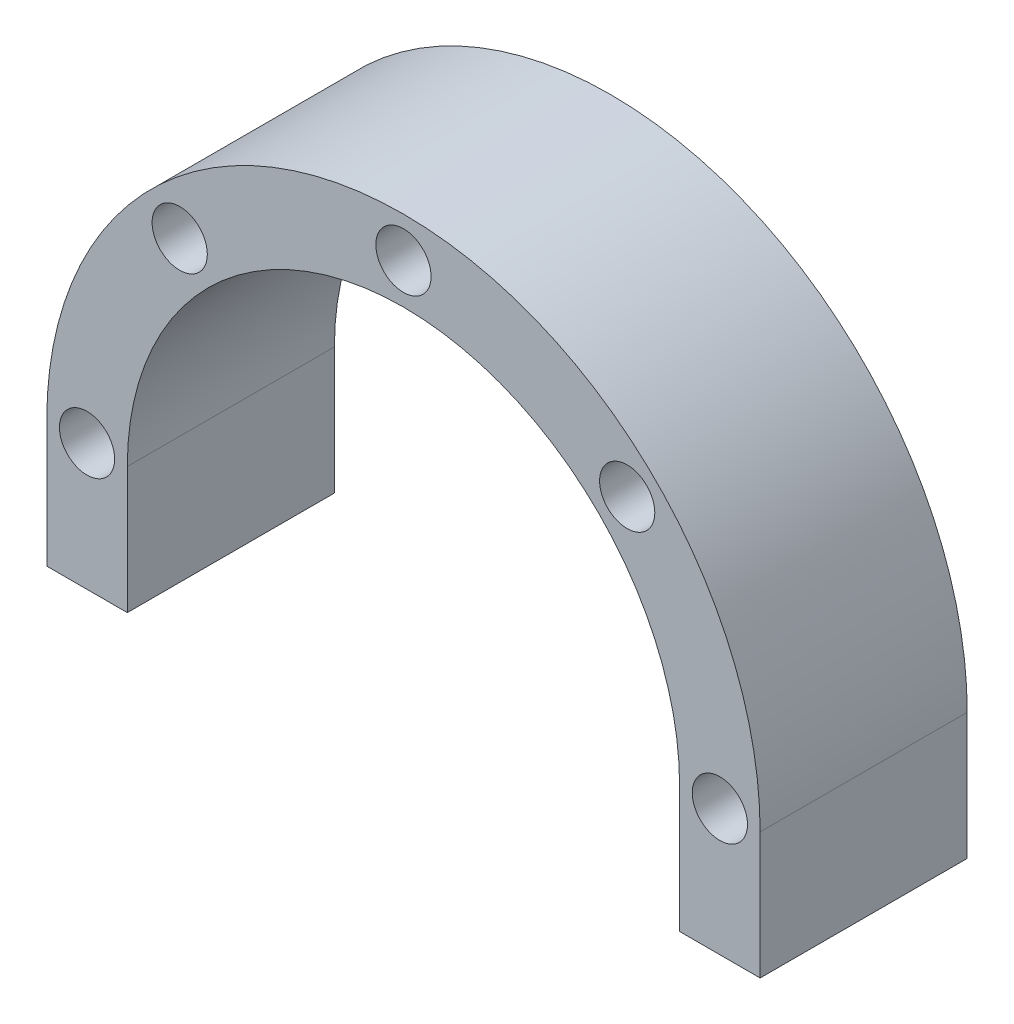
SolidWorks part; units mm, degrees
material "ABS"
ref_plane "正面" through (0, 0, 0) normal (0, 0, 1) x (1, 0, 0)
ref_plane "平面" through (0, 0, 0) normal (0, 1, 0) x (1, 0, 0)
ref_plane "右側面" through (0, 0, 0) normal (1, 0, 0) x (0, 0, -1)
sketch "ｽｹｯﾁ1" plane through (0, 0, 0) normal (0, 0, 1) x (1, 0, 0)
  line L0 (0, -1000) -> (0, 49000) construction
  line L1 (-31, -11) -> (31, -11)
  line L2 (-31, 0) -> (-31, -11)
  line L4 (31, -11) -> (31, 0)
  circle A0 centre (0, 0) radius 31 construction
  arc A2 (-31, 0) -> (31, 0) centre (0, 0) cw
  point P3 (0, -31)
  dimension "D1" = 62
  dimension "D2" = 20
extrude "ﾎﾞｽ - 押し出し1" add sketch "ｽｹｯﾁ1" along normal blind 18 contours A2 L2 L1 L4
sketch "ｽｹｯﾁ2" plane through (0, 0, 18) normal (0, 0, 1) x (1, 0, 0)
  line L4 (-31, -11) -> (31, -11) construction
  line L9 (-24, 0) -> (-24, -11)
  line L11 (24, -11) -> (24, 0)
  line L12 (24, -11) -> (-24, -11)
  arc A1 (31, 0) -> (-31, 0) centre (0, 0) ccw construction
  arc A3 (24, 0) -> (-24, 0) centre (0, 0) ccw
  dimension "D1" = 24
extrude "ｶｯﾄ - 押し出し1" cut sketch "ｽｹｯﾁ2" against normal through all
hole_wizard "M4 すきま穴2" positions "ｽｹｯﾁ3" profile "ｽｹｯﾁ4" hole size "M4" standard "JIS" end condition through all
sketch "ｽｹｯﾁ3" plane through (0, 0, 18) normal (0, 0, 1) x (1, 0, 0)
  point P0 (0, 27.5)
  dimension "D1" = 27.5
sketch "ｽｹｯﾁ4" plane through (0, 27.5, 18) normal (1, 0, 0) x (0, -1, 0)
  line L0 (0, 0) -> (0, 18)
  line L1 (0, 18) -> (2.4, 18)
  line L2 (2.4, 18) -> (2.4, 0)
  line L5 (2.4, 0) -> (0, 0)
  line L11 (0, -6.35) -> (0, 107.95) construction
  dimension "通し穴の直径" = 4.8
  dimension "通し穴の深さ" = 18
pattern_circular "円形ﾊﾟﾀｰﾝ1" count 8 over 360 about axis through (0, 0, 0) along (0, 0, 1) skipping 3, 4, 5 of "M4 すきま穴2"
